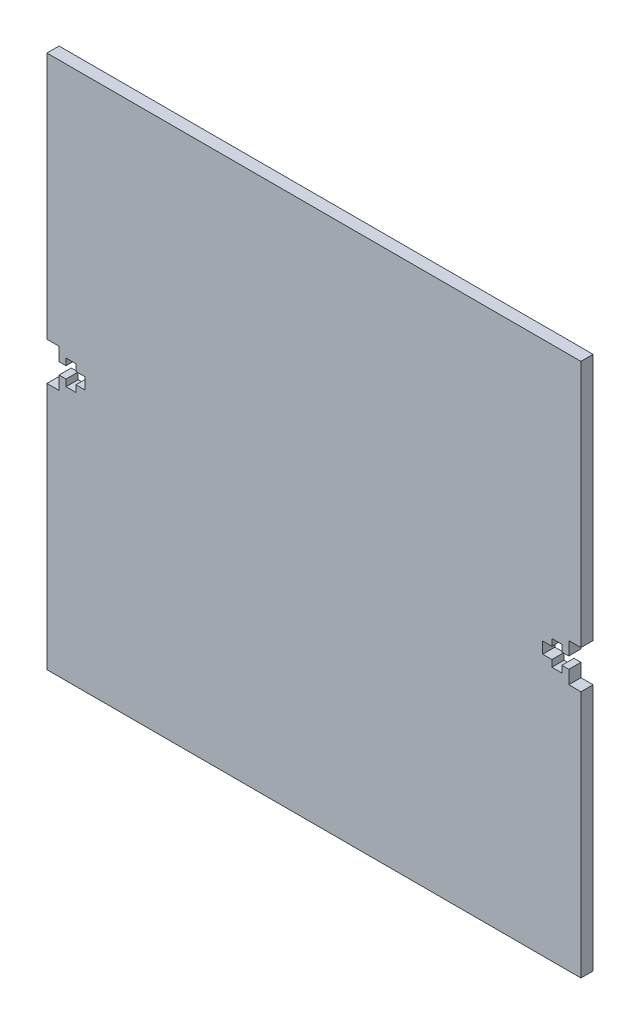
SolidWorks part; units mm, degrees
ref_plane "Front Plane" through (0, 0, 0) normal (0, 0, 1) x (1, 0, 0)
ref_plane "Top Plane" through (0, 0, 0) normal (0, 1, 0) x (1, 0, 0)
ref_plane "Right Plane" through (0, 0, 0) normal (1, 0, 0) x (0, 0, -1)
sketch "Sketch1" plane through (0, 0, 0) normal (0, 0, 1) x (1, 0, 0)
  line L1 (-69.85, 69.85) -> (69.85, 69.85)
  line L2 (-69.85, 69.85) -> (-69.85, -69.85)
  line L3 (-69.85, -69.85) -> (69.85, -69.85)
  line L4 (69.85, 69.85) -> (69.85, -69.85)
  line L5 (-69.85, 69.85) -> (69.85, -69.85) construction
  line L6 (-69.85, -69.85) -> (69.85, 69.85) construction
  point P0 (0, 0)
  dimension "D1" = 139.7
  dimension "D2" = 139.7
extrude "Boss-Extrude1" add sketch "Sketch1" along normal blind 3.18
sketch "Sketch21" plane through (-38.3956, -37.1996, 0) normal (0, 0, -1) x (-1, 0, 0)
  line L0 (31.4544, 37.1996) -> (21.4544, 37.1996) construction
  line L1 (31.4544, -32.6504) -> (31.4544, 107.0496) construction
  line L2 (28.2744, 35.6996) -> (28.2744, 32.1996)
  line L3 (31.4544, 42.1996) -> (31.4544, 32.1996)
  line L4 (31.4544, 42.1996) -> (28.2744, 42.1996)
  line L5 (28.2744, 42.1996) -> (28.2744, 38.6996)
  line L6 (31.4544, 32.1996) -> (28.2744, 32.1996)
  line L8 (28.2744, 38.6996) -> (26.4544, 38.6996)
  line L9 (21.4544, 38.6996) -> (21.4544, 35.6996)
  line L10 (28.2744, 35.6996) -> (26.4544, 35.6996)
  line L11 (26.4544, 40.4496) -> (26.4544, 33.9496) construction
  line L12 (26.4544, 40.4496) -> (23.8544, 40.4496)
  line L13 (23.8544, 40.4496) -> (23.8544, 38.6996)
  line L14 (26.4544, 33.9496) -> (23.8544, 33.9496)
  line L15 (23.8544, 38.6996) -> (21.4544, 38.6996)
  line L16 (23.8544, 35.6996) -> (23.8544, 33.9496)
  line L17 (23.8544, 35.6996) -> (21.4544, 35.6996)
  line L18 (26.4544, 40.4496) -> (26.4544, 38.6996)
  line L19 (26.4544, 33.9496) -> (26.4544, 35.6996)
  point P17 (26.4544, 37.1996)
  dimension "D1" = 3.18
  dimension "D2" = 10
  dimension "D3" = 3
  dimension "D4" = 2.6
  dimension "D5" = 6.5
  dimension "D6" = 10
extrude "Cut-Extrude1" cut sketch "Sketch21" against normal through all
other "TholeCutmkIVtru<1>"
sketch "Sketch22" plane through (0, 0, 0) normal (0, 0, -1) x (-1, 0, 0)
  line L0 (-66.67, -5) -> (-69.85, -5)
  line L9 (-69.85, 5) -> (-66.67, 5)
  line L19 (-69.85, 0) -> (-59.85, 0) construction
  line L20 (-69.85, -69.85) -> (-69.85, 69.85) construction
  line L21 (-64.85, -3.25) -> (-64.85, -1.5)
  line L22 (-64.85, 3.25) -> (-64.85, 1.5)
  line L23 (-62.25, -1.5) -> (-59.85, -1.5)
  line L24 (-62.25, -1.5) -> (-62.25, -3.25)
  line L25 (-62.25, 1.5) -> (-59.85, 1.5)
  line L26 (-64.85, -3.25) -> (-62.25, -3.25)
  line L27 (-62.25, 3.25) -> (-62.25, 1.5)
  line L28 (-64.85, 3.25) -> (-62.25, 3.25)
  line L29 (-66.67, -1.5) -> (-64.85, -1.5)
  line L30 (-59.85, 1.5) -> (-59.85, -1.5)
  line L31 (-66.67, 1.5) -> (-64.85, 1.5)
  line L32 (-66.67, 5) -> (-66.67, 1.5)
  line L33 (-66.67, -1.5) -> (-66.67, -5)
  line L34 (-69.85, -5) -> (-69.85, 5)
  line L35 (69.85, -69.85) -> (-69.85, -69.85) construction
  line L36 (-69.85, 69.85) -> (69.85, 69.85) construction
  dimension "D1" = 2.6
  dimension "D2" = 1.75
  dimension "D3" = 2.4
  dimension "D4" = 1.82
  dimension "D5" = 3
  dimension "D6" = 10
  dimension "D7" = 3
  dimension "D8" = 2.4
  dimension "D9" = 1.75
  dimension "D10" = 2.6
  dimension "D11" = 10
  dimension "D12" = 1.75
  dimension "D13" = 1.82
  dimension "D14" = 3.5
  dimension "D15" = 3.18
extrude "Cut-Extrude3" cut sketch "Sketch22" against normal blind 10
